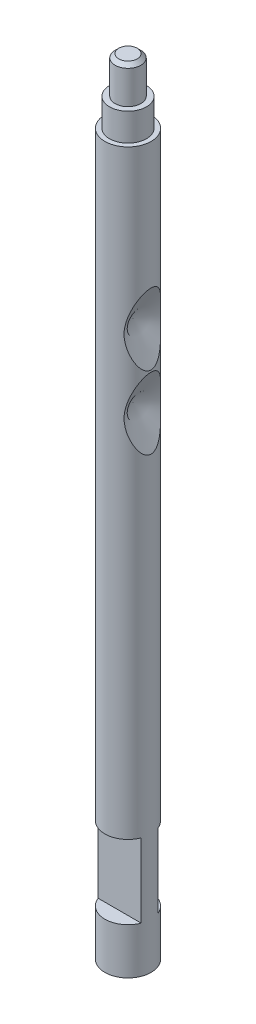
SolidWorks part; units mm, degrees
ref_plane "Front Plane" through (0, 0, 0) normal (0, 0, 1) x (1, 0, 0)
ref_plane "Top Plane" through (0, 0, 0) normal (0, 1, 0) x (1, 0, 0)
ref_plane "Right Plane" through (0, 0, 0) normal (1, 0, 0) x (0, 0, -1)
sketch "Sketch1" plane through (0, 0, 0) normal (0, 1, 0) x (1, 0, 0)
  circle A0 centre (0, 0) radius 1.25
  dimension "D1" = 2.5
extrude "Boss-Extrude1" add sketch "Sketch1" along normal blind 42.5
sketch "Sketch2" plane through (0, 42.5, 0) normal (0, 1, 0) x (1, 0, 0)
  circle A0 centre (0, 0) radius 1
  dimension "D1" = 2
extrude "Cut-Extrude1" cut sketch "Sketch2" against normal blind 3.5 flip side to cut
sketch "Sketch3" plane through (0, 42.5, 0) normal (0, 1, 0) x (1, 0, 0)
  circle A0 centre (0, 0) radius 0.7
  dimension "D1" = 1.4
extrude "Cut-Extrude2" cut sketch "Sketch3" against normal blind 2 flip side to cut
cosmetic thread "Cosmetic Thread1" parameters "D2"=1.057
chamfer "Chamfer1" distance 0.2 angle 45 1 edges at (0, 42.5, 0.7)
sketch "Sketch4" plane through (0, 0, 0) normal (1, 0, 0) x (0, 0, -1)
  line L0 (0, 0) -> (0, 15.8008) construction
  line L1 (-1.25, 0) -> (1.25, 0) construction
  line L2 (0.45, 6.5) -> (1.25, 6.5)
  line L3 (0.45, 6.5) -> (0.45, 2.5)
  line L4 (0.45, 2.5) -> (1.25, 2.5)
  line L5 (-1.25, 2.5) -> (-1.25, 6.5)
  line L6 (-0.45, 2.5) -> (-1.25, 2.5)
  line L7 (-0.45, 6.5) -> (-0.45, 2.5)
  line L8 (-0.45, 6.5) -> (-1.25, 6.5)
  line L9 (1.25, 0) -> (1.25, 39) construction
  line L10 (1.25, 2.5) -> (1.25, 6.5)
  dimension "D1" = 0.9
  dimension "D2" = 2.5
  dimension "D3" = 4
extrude "Cut-Extrude3" cut sketch "Sketch4" against normal through all both and the other way through all
sketch "Sketch5" plane through (0, 0, 0) normal (0, 0, 1) x (1, 0, 0)
  line L0 (0, 42.5) -> (0, 28.4235) construction
  line L1 (0.5, 42.5) -> (-0.5, 42.5) construction
  line L2 (1.25, 32.1234) -> (0.27, 30.2)
  line L3 (1.25, 0) -> (1.25, 39) construction
  line L4 (0.27, 30.2) -> (1.25, 28.2766) construction
  line L5 (0.27, 30.2) -> (1.8893, 30.2) construction
  line L6 (1.25, 30.2) -> (1.25, 32.1234)
  line L7 (0.27, 30.2) -> (1.25, 30.2)
  line L8 (1.25, 0) -> (1.25, 39) construction
  dimension "D1" = 126
  dimension "D2" = 0.98
  dimension "D3" = 8.8
revolve "Cut-Revolve2" cut sketch "Sketch5" angle 360 about L5
pattern_linear "LPattern1" count 2 spacing 3.95 along (0, -1, 0) of "Cut-Revolve2"
